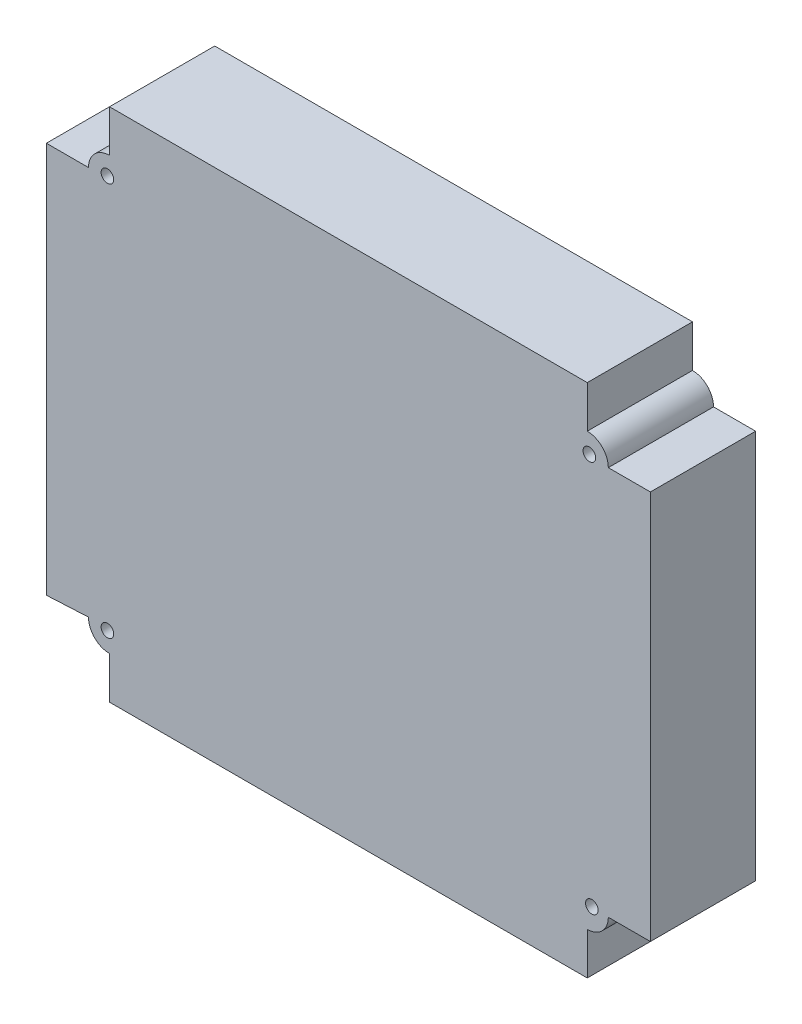
SolidWorks part; units mm, degrees
ref_plane "前视基准面" through (0, 0, 0) normal (0, 0, 1) x (1, 0, 0)
ref_plane "上视基准面" through (0, 0, 0) normal (0, 1, 0) x (1, 0, 0)
ref_plane "右视基准面" through (0, 0, 0) normal (1, 0, 0) x (0, 0, -1)
sketch "草图1" plane through (0, 0, 0) normal (0, 0, 1) x (1, 0, 0)
  line L0 (-119.4863, 97.5) -> (-129.4863, 97.5)
  line L5 (-119.4863, 102.5) -> (4.0137, 0) construction
  line L6 (-119.4863, 0) -> (4.0137, 102.5) construction
  line L7 (-129.4863, 97.5) -> (-129.4863, 4.5)
  line L8 (-129.4863, 4.5) -> (-119.4863, 5)
  line L9 (-114.4863, 0) -> (-114.4863, -10)
  line L10 (-114.4863, -10) -> (-0.9863, -10)
  line L11 (-0.9863, -10) -> (-0.9863, 0)
  line L12 (4.0137, 5) -> (14.0137, 5)
  line L13 (14.0137, 5) -> (14.0137, 97.5)
  line L14 (14.0137, 97.5) -> (4.0137, 97.5)
  line L15 (-0.9863, 102.5) -> (-0.9863, 112.5)
  line L16 (-0.9863, 112.5) -> (-114.4863, 112.5)
  line L17 (-114.4863, 112.5) -> (-114.4863, 102.5)
  circle A0 centre (-114.9863, 98) radius 1.5
  circle A1 centre (-114.9863, 4.5) radius 1.5
  circle A2 centre (0.0957, 5.2012) radius 1.5
  circle A3 centre (-0.4863, 98) radius 1.5
  arc A4 (-119.4863, 5) -> (-114.4863, 0) centre (-114.4863, 5) ccw
  arc A5 (-0.9863, 0) -> (4.0137, 5) centre (-0.9863, 5) ccw
  arc A6 (-0.9863, 102.5) -> (4.0137, 97.5) centre (-0.9863, 97.5) cw
  arc A7 (-114.4863, 102.5) -> (-119.4863, 97.5) centre (-114.4863, 97.5) ccw
  point P0 (-57.7363, 51.25)
  dimension "D7" = 5
  dimension "D3" = 3
  dimension "D1" = 123.5
  dimension "D2" = 102.5
extrude "凸台-拉伸1" add sketch "草图1" along normal blind 25
